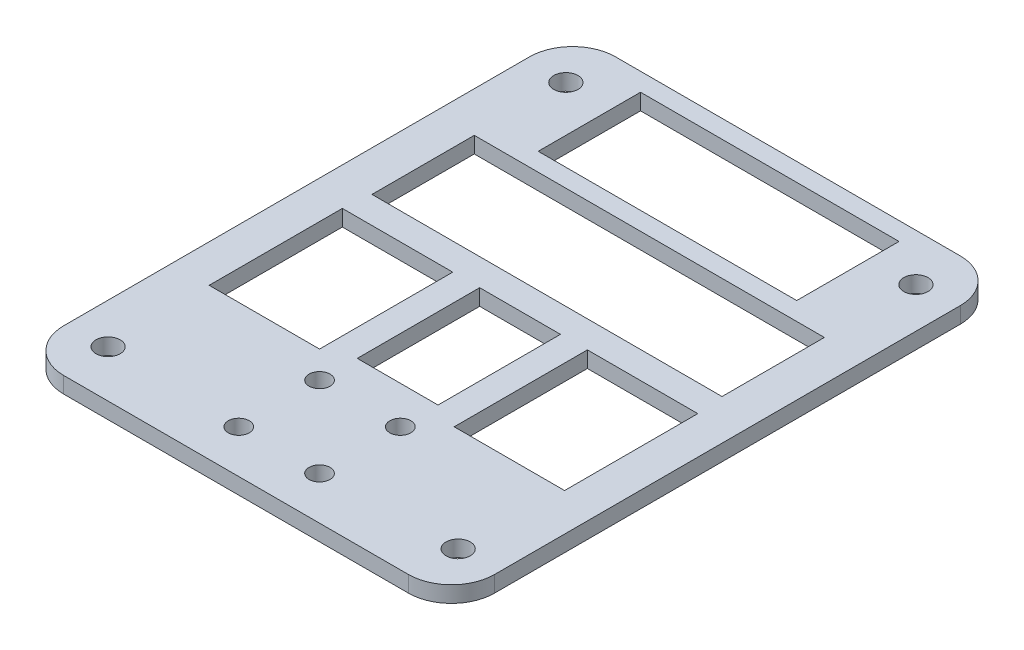
SolidWorks part; units mm, degrees
material "PF"
ref_plane "Plan de face" through (0, 0, 0) normal (0, 0, 1) x (1, 0, 0)
ref_plane "Plan de dessus" through (0, 0, 0) normal (0, 1, 0) x (1, 0, 0)
ref_plane "Plan de droite" through (0, 0, 0) normal (1, 0, 0) x (0, 0, -1)
sketch "Esquisse1" plane through (0, 0, 0) normal (0, 1, 0) x (1, 0, 0)
  circle A0 centre (0, 0) radius 65
  dimension "D1" = 130
extrude "disque" add sketch "Esquisse1" along normal blind 3
sketch "Esquisse3" plane through (0, 3, 0) normal (0, 1, 0) x (1, 0, 0)
  line L0 (0, 0) -> (0, 63.5107) construction
  line L1 (-40, 100) -> (-40, -100)
  line L2 (-40, -100) -> (-70.4664, -100)
  line L3 (-70.4664, -100) -> (-70.4664, 100)
  line L4 (-70.4664, 100) -> (-40, 100)
  line L5 (40, -100) -> (70.4664, -100)
  line L6 (70.4664, -100) -> (70.4664, 100)
  line L7 (70.4664, 100) -> (40, 100)
  line L8 (40, 100) -> (40, -100)
  line L9 (-40, 0) -> (0, 0) construction
  dimension "D1" = 40
  dimension "D2" = 200
extrude "cotés" cut sketch "Esquisse3" against normal through all
sketch "Esquisse4" plane through (0, 3, 0) normal (0, 1, 0) x (1, 0, 0)
  line L0 (-40, -28.7652) -> (40, -28.7652) construction
  line L1 (0, 65) -> (0, -65) construction
  line L2 (-40, 51.2348) -> (53.9104, 51.2348) construction
  line L3 (-40, 26.2348) -> (58.169, 26.2348) construction
  line L4 (-40, -51.2348) -> (-40, 51.2348) construction
  arc A0 (40, 51.2348) -> (-40, 51.2348) centre (0, 0) ccw construction
  arc A1 (-40, -51.2348) -> (40, -51.2348) centre (0, 0) ccw construction
  point P2 (0, -28.7652)
  point P11 (0, 58.6194)
  dimension "D1" = 80
  dimension "D2" = 55
sketch "Esquisse10" plane through (0, 3, 0) normal (0, 1, 0) x (1, 0, 0)
  line L1 (32.5, -42.5) -> (-32.5, -42.5)
  line L2 (32.5, -42.5) -> (32.5, 42.5)
  line L3 (32.5, 42.5) -> (-32.5, 42.5)
  line L4 (-32.5, -42.5) -> (-32.5, 42.5)
  line L5 (32.5, -42.5) -> (-32.5, 42.5) construction
  line L6 (32.5, 42.5) -> (-32.5, -42.5) construction
  point P0 (0, 0)
  dimension "D1" = 85
  dimension "D2" = 65
ref_plane "Plan1" through (0, 0, 0) normal (-1, 0, 0) x (0, 0, 1)
hole_wizard "Dégagement M42" positions "Esquisse12" profile "Esquisse13" hole size "M4" standard "Iso" end condition through all
sketch "Esquisse12" plane through (0, 3, 0) normal (0, 1, 0) x (1, 0, 0)
  point P0 (-32.5, 42.5)
  point P3 (32.5, 42.5)
  point P6 (32.5, -42.5)
  point P9 (-32.5, -42.5)
sketch "Esquisse13" plane through (-32.5, 3, -42.5) normal (1, 0, 0) x (0, 0, 1)
  line L0 (0, 0) -> (0, 3)
  line L1 (0, 3) -> (2.25, 3)
  line L2 (2.25, 3) -> (2.25, 0)
  line L5 (2.25, 0) -> (0, 0)
  line L11 (0, -6.35) -> (0, 107.95) construction
  dimension "Diamètre du perçage jusqu'au prochain" = 4.5
  dimension "Profondeur du perçage jusqu'au prochain" = 3
ref_plane "Plan2" through (0, 0, 0) normal (-1, 0, 0) x (0, 0, 1)
sketch "Esquisse15" plane through (0, 0, 0) normal (0, -1, 0) x (1, 0, 0)
  line L1 (40, 51.2348) -> (-49.8632, 51.2348)
  line L2 (40, 51.2348) -> (40, 83.331)
  line L3 (40, 83.331) -> (-49.8632, 83.331)
  line L4 (-49.8632, 51.2348) -> (-49.8632, 83.331)
extrude "Enlèv. mat.-Extru.1" cut sketch "Esquisse15" against normal through all
ref_plane "Plan3" through (0, 0, 0) normal (0, -1, 0) x (-1, 0, 0)
sketch "emplacement compos" plane through (0, 0, 0) normal (0, -1, 0) x (-1, 0, 0)
  line L0 (0, 72.5668) -> (0, -66.1044) construction
  line L1 (-40, -5.1284) -> (64.5168, -5.1284) construction
  line L2 (-40, 51.2348) -> (-40, -51.2348) construction
  line L3 (-40, 51.2348) -> (63.3599, 51.2348) construction
  line L4 (32.5, 6.5) -> (-32.5, 6.5)
  line L5 (32.5, 6.5) -> (32.5, 25.5)
  line L6 (32.5, 25.5) -> (-32.5, 25.5)
  line L7 (-32.5, 6.5) -> (-32.5, 25.5)
  line L8 (32.5, 6.5) -> (-32.5, 25.5) construction
  line L9 (32.5, 25.5) -> (-32.5, 6.5) construction
  line L10 (24, 28.8674) -> (-24, 28.8674)
  line L11 (24, 28.8674) -> (24, 47.8674)
  line L12 (24, 47.8674) -> (-24, 47.8674)
  line L13 (-24, 28.8674) -> (-24, 47.8674)
  line L14 (24, 28.8674) -> (-24, 47.8674) construction
  line L15 (24, 47.8674) -> (-24, 28.8674) construction
  line L16 (-40, 16) -> (-32.5, 16) construction
  line L17 (32.5, 38.3674) -> (40, 38.3674) construction
  line L18 (40, -51.2348) -> (40, 51.2348) construction
  line L19 (-24, 38.3674) -> (-40, 38.3674) construction
  line L20 (25.5, -47.8674) -> (-25.5, -47.8674)
  line L21 (25.5, -47.8674) -> (25.5, 3.1326)
  line L22 (25.5, 3.1326) -> (-25.5, 3.1326)
  line L23 (-25.5, -47.8674) -> (-25.5, 3.1326)
  line L24 (25.5, -47.8674) -> (-25.5, 3.1326) construction
  line L25 (25.5, 3.1326) -> (-25.5, -47.8674) construction
  line L26 (24, 38.3674) -> (40, 38.3674) construction
  line L27 (-25.5, -22.3674) -> (-40, -22.3674) construction
  line L28 (25.5, -22.3674) -> (40, -22.3674) construction
  line L29 (40, -51.2348) -> (-40, -51.2348) construction
  line L30 (-11.3137, 51.2348) -> (-11.3137, 47.8674) construction
  line L31 (11.3137, -36.3674) -> (-11.3137, -36.3674)
  line L32 (11.3137, -36.3674) -> (11.3137, -8.3674)
  line L33 (11.3137, -8.3674) -> (-11.3137, -8.3674)
  line L34 (-11.3137, -36.3674) -> (-11.3137, -8.3674)
  line L35 (11.3137, -36.3674) -> (-11.3137, -8.3674) construction
  line L36 (11.3137, -8.3674) -> (-11.3137, -36.3674) construction
  line L37 (-11.3137, 28.8674) -> (-11.3137, 25.5) construction
  line L38 (-11.3137, 6.5) -> (-11.3137, 3.1326) construction
  line L39 (-11.3137, -47.8674) -> (-11.3137, -51.2348) construction
  line L41 (40, 51.2348) -> (-80.2005, 51.2348)
  line L42 (40, 51.2348) -> (40, 81.8608)
  line L43 (40, 81.8608) -> (-80.2005, 81.8608)
  line L44 (-80.2005, 51.2348) -> (-80.2005, 81.8608)
  point P7 (0, 16)
  point P12 (0, 38.3674)
  point P26 (0, -22.3674)
  point P40 (0, -22.3674)
  dimension "D3" = 19
  dimension "D4" = 65
  dimension "D5" = 48
  dimension "D6" = 51
  dimension "D8" = 36
  dimension "D9" = 28
extrude "Enlèv. mat.-Extru.2" cut sketch "emplacement compos" against normal through all contours L13 L10 L11 L12 | L7 L4 L5 L6 | L44 L41 L42 L43
fillet "Congé1" radius 8 4 edges at (-40, 1.5, 51.2348) (40, 1.5, 51.2348) (40, 1.5, -51.2348) (-40, 1.5, -51.2348)
sketch "Esquisse16" plane through (0, 3, 0) normal (0, 1, 0) x (1, 0, 0)
  line L0 (-32, -51.2348) -> (32, -51.2348) construction
  line L1 (-7.5, -43.2348) -> (7.5, -43.2348)
  line L2 (-7.5, -43.2348) -> (-7.5, -28.2348)
  line L3 (-7.5, -28.2348) -> (7.5, -28.2348)
  line L4 (7.5, -43.2348) -> (7.5, -28.2348)
  line L5 (-7.5, -43.2348) -> (7.5, -28.2348) construction
  line L6 (-7.5, -28.2348) -> (7.5, -43.2348) construction
  point P0 (0, -35.7348)
  dimension "D1" = 8
  dimension "D2" = 15
  dimension "D3" = 15
hole_wizard "Dégagement M3.51" positions "Esquisse18" profile "Esquisse17" hole size "M3.5" standard "Iso"
sketch "Esquisse18" plane through (0, 3, 0) normal (0, 1, 0) x (1, 0, 0)
  point P0 (-7.5, -28.2348)
  point P3 (7.5, -28.2348)
  point P6 (7.5, -43.2348)
  point P9 (-7.5, -43.2348)
sketch "Esquisse17" plane through (-7.5, 3, 28.2348) normal (1, 0, 0) x (0, 0, 1)
  line L0 (0, 0) -> (0, 4.1717)
  line L1 (0, 4.1717) -> (1.95, 3)
  line L2 (1.95, 3) -> (1.95, 0)
  line L5 (1.95, 0) -> (0, 0)
  line L10 (0, 4.1717) -> (-1.95, 3) construction
  line L11 (0, -6.35) -> (0, 107.95) construction
  dimension "Diamètre du perçage" = 3.9
  dimension "Profondeur du perçage" = 3
  dimension "Angle de pointe" = 118
sketch "Esquisse19" plane through (0, 3, 0) normal (0, 1, 0) x (1, 0, 0)
  line L0 (-32.5, 6.5) -> (32.5, 6.5) construction
  line L1 (-33, -23.2348) -> (-12.5, -23.2348)
  line L2 (-33, -23.2348) -> (-33, 1.5)
  line L3 (-33, 1.5) -> (-12.5, 1.5)
  line L4 (-12.5, -23.2348) -> (-12.5, 1.5)
  line L5 (-33, -23.2348) -> (-12.5, 1.5) construction
  line L6 (-33, 1.5) -> (-12.5, -23.2348) construction
  line L7 (-40, -43.2348) -> (-40, 43.2348) construction
  circle A0 centre (-7.5, -28.2348) radius 1.95 construction
  point P0 (-22.75, -10.8674)
  dimension "D1" = 5
  dimension "D2" = 5
  dimension "D3" = 5
  dimension "D4" = 7
extrude "Enlèv. mat.-Extru.3" cut sketch "Esquisse19" against normal through all
sketch "Esquisse20" plane through (0, 3, 0) normal (0, 1, 0) x (1, 0, 0)
  line L0 (-32, 51.2348) -> (32, 51.2348) construction
  line L1 (0, 0) -> (0, 69.6266) construction
  point P0 (0, 0)
  point P1 (0, 51.2348)
sketch "Esquisse21" plane through (0, 0, -51.2348) normal (0, 0, -1) x (-1, 0, 0)
  point P0 (0, 0)
ref_plane "Plan4" through (0, 0, 0) normal (-1, 0, 0) x (0, 0, 1)
mirror "Symétrie1" about plane through (0, 0, 0) normal (-1, 0, 0) of "Enlèv. mat.-Extru.3"
sketch "Esquisse22" plane through (0, 3, 0) normal (0, 1, 0) x (1, 0, 0)
  line L0 (-32.5, 6.5) -> (32.5, 6.5) construction
  line L1 (-7.5, -21.2348) -> (7.5, -21.2348)
  line L2 (-7.5, -21.2348) -> (-7.5, 1.5)
  line L3 (-7.5, 1.5) -> (7.5, 1.5)
  line L4 (7.5, -21.2348) -> (7.5, 1.5)
  line L5 (-7.5, -21.2348) -> (7.5, 1.5) construction
  line L6 (-7.5, 1.5) -> (7.5, -21.2348) construction
  line L7 (33, -23.2348) -> (12.5, -23.2348) construction
  line L8 (12.5, -23.2348) -> (12.5, 1.5) construction
  line L9 (-12.5, -23.2348) -> (-12.5, 1.5) construction
  point P0 (0, -9.8674)
  dimension "D1" = 5
  dimension "D2" = 2
  dimension "D3" = 5
  dimension "D4" = 5
extrude "Enlèv. mat.-Extru.4" cut sketch "Esquisse22" against normal through all
